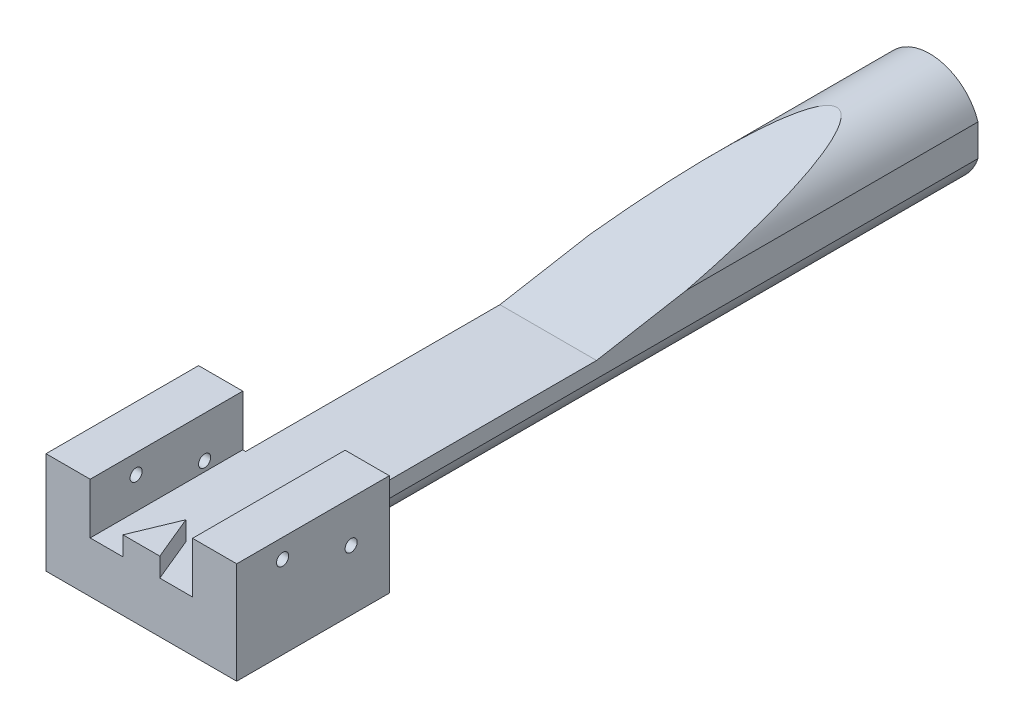
SolidWorks part; units mm, degrees
material "Copper"
ref_plane "Ebene vorne" through (0, 0, 0) normal (0, 0, 1) x (1, 0, 0)
ref_plane "Ebene oben" through (0, 0, 0) normal (0, 1, 0) x (1, 0, 0)
ref_plane "Ebene rechts" through (0, 0, 0) normal (1, 0, 0) x (0, 0, -1)
sketch "Sketch1" plane through (0, 0, 0) normal (0, 0, 1) x (1, 0, 0)
  circle A0 centre (0, 0) radius 4
extrude "Boss-Extrude1" add sketch "Sketch1" along normal blind 50
sketch "Sketch2" plane through (0, 0, 50) normal (0, 0, 1) x (1, 0, 0)
  line L1 (-7.5, 4) -> (7.5, 4)
  line L2 (-7.5, 4) -> (-7.5, -4)
  line L3 (-7.5, -4) -> (7.5, -4)
  line L4 (7.5, 4) -> (7.5, -4)
  circle A0 centre (0, 0) radius 4 construction
  point P7 (0, -4)
extrude "Boss-Extrude2" add sketch "Sketch2" along direction (0, 0, 1) on the side of the normal blind 12
sketch "Sketch3" plane through (0, 4, 0) normal (0, 1, 0) x (1, 0, 0)
  line L1 (-4.025, -30) -> (4.025, -30)
  line L2 (-4.025, -30) -> (-4.025, -62)
  line L3 (-4.025, -62) -> (4.025, -62)
  line L4 (4.025, -30) -> (4.025, -62)
  line L5 (7.5, -62) -> (-7.5, -62) construction
  point P12 (0, -62)
extrude "Cut-Extrude1" cut sketch "Sketch3" against normal blind 4
sketch "Sketch4" plane through (0, 0, 30) normal (0, 0, 1) x (1, 0, 0)
  line L1 (-10, 0) -> (10, 0)
  arc A0 (-10, 0) -> (10, 0) centre (0, 0) cw
extrude "Cut-Extrude3" cut sketch "Sketch4" against normal blind 30 draft 10
sketch "Sketch6" plane through (0, 0, 0) normal (0, 1, 0) x (1, 0, 0)
  line L0 (-1.4497, -62) -> (0, -58.5)
  line L1 (0, -58.5) -> (1.4497, -62)
  line L2 (1.4497, -62) -> (-1.4497, -62)
  line L4 (-4.025, -62) -> (4.025, -62) construction
  line L5 (4, -30) -> (-4, -30) construction
  point P14 (0, -30)
  dimension "D1" = 45
  dimension "D2" = 3.5
extrude "Boss-Extrude3" add sketch "Sketch6" along normal blind 1.5
hole_wizard "Tap Drill for M1.2x0.25 Tap2" positions "Sketch8" profile "Sketch9" hole size "M1.2x0.25" standard "ANSI Metric"
sketch "Sketch8" plane through (-7.5, 0, 0) normal (-1, 0, 0) x (0, 0, 1)
  line L0 (62, 4) -> (50, 4) construction
  line L2 (50, 4) -> (50, -4) construction
  line L3 (62, 4) -> (62, -4) construction
  point P0 (53, 0.75)
  point P2 (58.3904, 2.5)
  dimension "D1" = 1.5
  dimension "D2" = 3.25
  dimension "D3" = 3
  dimension "D4" = 3.6096
sketch "Sketch9" plane through (-7.5, 0.75, 53) normal (0, 1, 0) x (0, 0, 1)
  line L0 (0, 0) -> (0, 15.2854)
  line L1 (0, 15.2854) -> (0.475, 15)
  line L2 (0.475, 15) -> (0.475, 0)
  line L5 (0.475, 0) -> (0, 0)
  line L10 (0, 15.2854) -> (-0.475, 15) construction
  line L11 (0, -5.1606) -> (0, 20.907) construction
  dimension "Hole Dia." = 0.95
  dimension "Hole Depth" = 15
  dimension "Drill Angle" = 118
hole_wizard "Tap Drill for M4x0.7 Tap1" positions "Sketch24" profile "Sketch25" hole size "M4x0.7" standard "ANSI Metric"
sketch "Sketch24" plane through (0, 0, 0) normal (0, 0, -1) x (-1, 0, 0)
  point P0 (0, 0)
sketch "Sketch25" plane through (0, 0, 0) normal (1, 0, 0) x (0, 1, 0)
  line L0 (0, 0) -> (0, 15.9914)
  line L1 (0, 15.9914) -> (1.65, 15)
  line L2 (1.65, 15) -> (1.65, 0)
  line L5 (1.65, 0) -> (0, 0)
  line L10 (0, 15.9914) -> (-1.65, 15) construction
  line L11 (0, -6.35) -> (0, 107.95) construction
  dimension "Hole Dia." = 3.3
  dimension "Hole Depth" = 15
  dimension "Drill Angle" = 118
sketch "Sketch26" plane through (0, 0, 0) normal (0, 0, -1) x (-1, 0, 0)
  line L0 (-7.5, 4) -> (-4.025, 4) construction
  line L1 (-4.025, 4) -> (-3.8, 4)
  line L2 (-4.025, 4) -> (-4.025, -4)
  line L3 (-4.025, -4) -> (-3.8, -4)
  line L4 (-3.8, 4) -> (-3.8, -4)
  line L5 (0, -4) -> (-7.5, -4) construction
  line L6 (-4.025, 0) -> (-4.025, 4) construction
  line L7 (4.025, 4) -> (3.8, 4)
  line L8 (4.025, 4) -> (4.025, -4)
  line L9 (4.025, -4) -> (3.8, -4)
  line L10 (3.8, 4) -> (3.8, -4)
  line L11 (4.025, 4) -> (4.025, 0) construction
  line L12 (4.025, 4) -> (7.5, 4) construction
  line L13 (7.5, -4) -> (0, -4) construction
extrude "Cut-Extrude4" cut sketch "Sketch26" against normal blind 50
